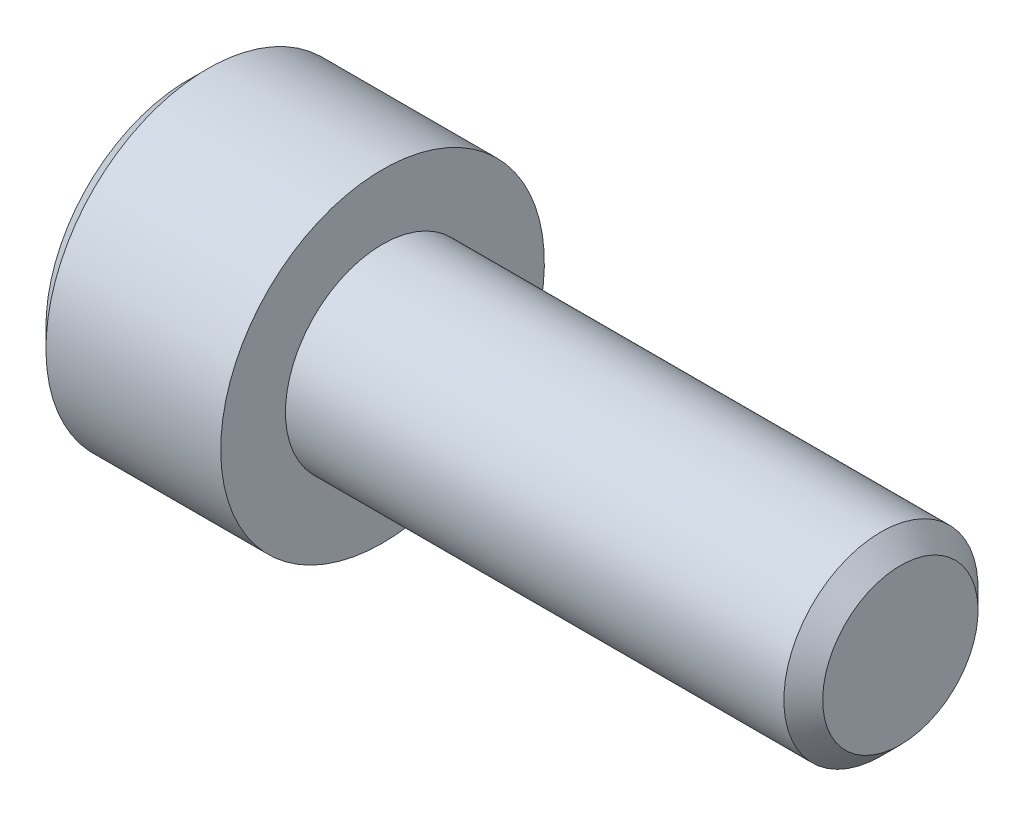
SolidWorks part; units mm, degrees
ref_plane "Front" through (0, 0, 0) normal (0, 0, 1) x (1, 0, 0)
ref_plane "Top" through (0, 0, 0) normal (0, 1, 0) x (1, 0, 0)
ref_plane "Right" through (0, 0, 0) normal (1, 0, 0) x (0, 0, -1)
ref_plane "Plane1" through (0, 0, 0) normal (0, 0, 1) x (1, 0, 0)
sketch "Sketch1" plane through (0, 0, 0) normal (0, 0, 1) x (1, 0, 0)
  line L0 (-6, 0) -> (-6, 4.4)
  line L1 (-6, 4.4) -> (-5.4, 5)
  line L2 (-5.4, 5) -> (0, 5)
  line L3 (0, 5) -> (0, 3)
  line L4 (0, 3) -> (16, 3)
  line L6 (16, 3) -> (16, 0)
  line L7 (16, 0) -> (-6, 0)
  line L8 (16, 0) -> (-6, 0) construction
  dimension "D1" = 16
  dimension "D2" = 3
  dimension "D3" = 5
  dimension "D4" = 6
revolve "Revolve1" add sketch "Sketch1" angle 360 about L8
ref_plane "Plane2" through (0, 0, 0) normal (0, 0, 1) x (1, 0, 0)
chamfer "Chamfer1" distance 0.6 angle 45 1 edges at (16, -3, 0)
sketch "Sketch2" plane through (0, 0, 0) normal (0, 0, 1) x (1, 0, 0)
  line L0 (-6, 0) -> (-6, 2.5)
  line L1 (-6, 2.5) -> (-3, 2.5)
  line L2 (-3, 2.5) -> (-2.3301, 0)
  line L3 (-2.3301, 0) -> (-6, 0)
  line L4 (-2.3301, 0) -> (-6, 0) construction
revolve "Cut-Revolve1" cut sketch "Sketch2" angle 360 about L4
ref_plane "Plane3" through (-6, 0, 0) normal (1, 0, 0) x (0, 0, -1)
sketch "Sketch3" plane through (-6, 0, 0) normal (1, 0, 0) x (0, 0, -1)
  line L0 (-2.5, 1.4434) -> (-2.5, -1.4434)
  line L1 (-2.5, -1.4434) -> (0, -2.8868)
  line L2 (0, -2.8868) -> (2.5, -1.4434)
  line L3 (2.5, -1.4434) -> (2.5, 1.4434)
  line L4 (2.5, 1.4434) -> (0, 2.8868)
  line L5 (0, 2.8868) -> (-2.5, 1.4434)
extrude "Cut-Extrude1" cut sketch "Sketch3" along normal blind 3
